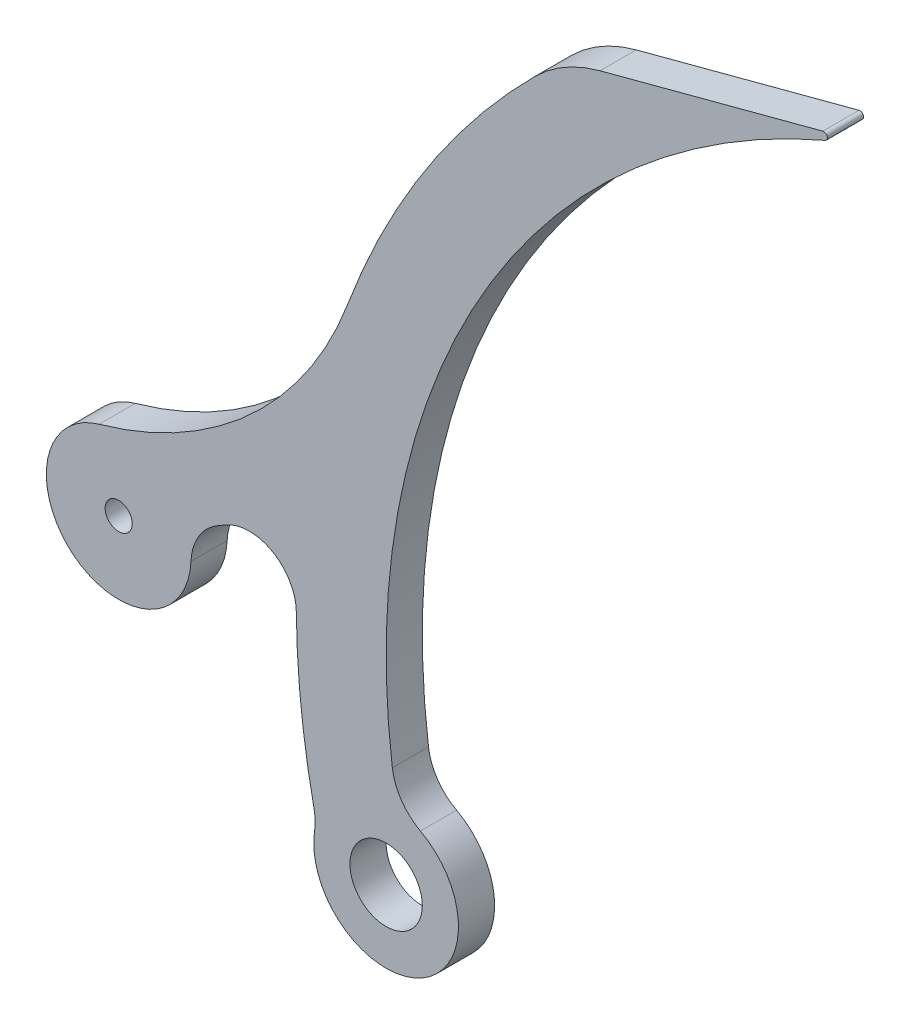
SolidWorks part; units mm, degrees
material "7075-T6 (SN)"
ref_plane "Front Plane" through (0, 0, 0) normal (0, 0, 1) x (1, 0, 0)
ref_plane "Top Plane" through (0, 0, 0) normal (0, 1, 0) x (1, 0, 0)
ref_plane "Right Plane" through (0, 0, 0) normal (1, 0, 0) x (0, 0, -1)
sketch "Sketch1" plane through (0, 0, 0) normal (0, 0, 1) x (1, 0, 0)
  line L0 (-200.3303, 96.2898) -> (-200.3303, 235.9666) construction
  line L1 (-187.8148, 239.2868) -> (-109.586, 260.0404)
  arc A0 (-81.744, 267.4267) -> (-246.2894, -66.3149) centre (-8.9225, 24.0895) ccw construction
  arc A1 (-210.6847, 226.1312) -> (-276.3666, 124.102) centre (-8.9225, 24.0895) ccw
  arc A2 (-108.7611, 257.6451) -> (-260.7436, -9.1091) centre (-8.9225, 24.0895) ccw
  arc A3 (-109.586, 260.0404) -> (-108.7611, 257.6451) centre (-109.2603, 258.8129) cw
  arc A4 (-210.6847, 226.1312) -> (-187.8148, 239.2868) centre (-174.7885, 190.1854) cw
  circle A5 centre (-262.9225, -45.7605) radius 12.7
  arc A6 (-288.0375, -41.9665) -> (-250.8851, -23.394) centre (-262.9225, -45.7605) ccw
  arc A7 (-250.8851, -23.394) -> (-260.7436, -9.1091) centre (-241.857, -6.6192) cw
  arc A8 (-288.0375, -41.9665) -> (-288.2386, -35.1675) centre (-306.8738, -39.121) ccw
  circle A9 centre (-356.8082, 19.4312) radius 4.7625
  arc A10 (-363.6645, 43.8884) -> (-331.4333, 18.3007) centre (-356.8082, 19.4312) ccw
  arc A11 (-363.6645, 43.8884) -> (-276.3666, 124.102) centre (-399.0087, 169.9648) ccw
  arc A12 (-321.8092, 34.0182) -> (-319.3626, 35.437) centre (-399.0087, 169.9648) ccw
  arc A13 (-294.4423, 21.3864) -> (-288.2386, -35.1675) centre (-8.9225, 24.0895) ccw
  arc A14 (-321.8092, 34.0182) -> (-331.4333, 18.3007) centre (-312.4022, 17.4529) ccw
  arc A15 (-294.4423, 21.3864) -> (-319.3626, 35.437) centre (-310.9515, 21.2301) ccw
  point P22 (-261.9539, 55.8348)
  dimension "D1" = 50.8
  dimension "D2" = 1.27
  dimension "D3" = 50.8
  dimension "D4" = 19.05
  dimension "D5" = 19.05
  dimension "D6" = 9.525
  dimension "D10" = 50.8
  dimension "D11" = 19.05
  dimension "D12" = 16.51
  dimension "D7" = 114.3
  dimension "D8" = 101.6
  dimension "D9" = 101.6
extrude "Boss-Extrude1" add sketch "Sketch1" along normal blind 12.7
